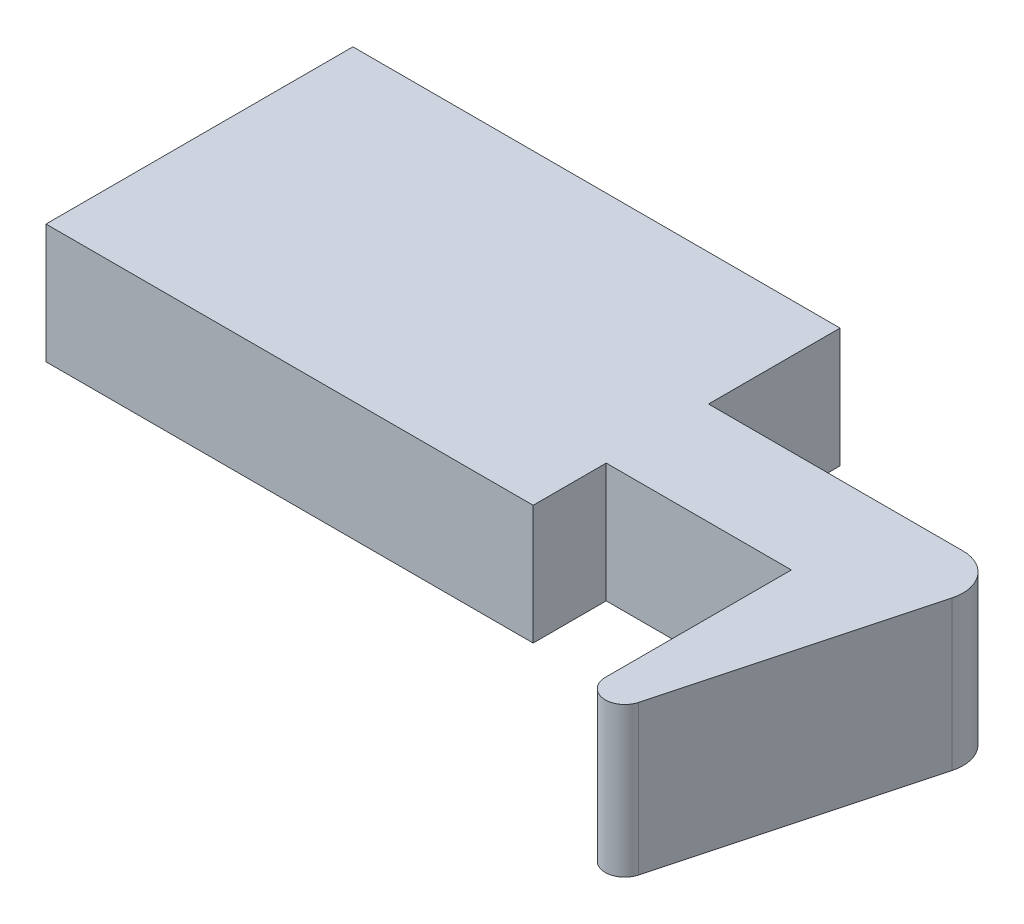
SolidWorks part; units mm, degrees
ref_plane "Front Plane" through (0, 0, 0) normal (0, 0, 1) x (1, 0, 0)
ref_plane "Top Plane" through (0, 0, 0) normal (0, 1, 0) x (1, 0, 0)
ref_plane "Right Plane" through (0, 0, 0) normal (1, 0, 0) x (0, 0, -1)
sketch "Sketch2" plane through (0, 0, 0) normal (0, 1, 0) x (1, 0, 0)
  line L0 (6.096, 5.334) -> (0, -17.4166)
  line L1 (0, 0) -> (-9.652, 0)
  line L2 (0, 0) -> (0, 5.334)
  line L3 (0, 5.334) -> (-9.652, 5.334)
  line L4 (-9.652, 0) -> (-9.652, 5.334)
  line L5 (0, 5.334) -> (6.096, 5.334)
  line L6 (0, 5.334) -> (0, -17.4166)
  line L10 (-9.652, -3.81) -> (-35.052, -3.81)
  line L11 (-9.652, -3.81) -> (-9.652, 12.192)
  line L12 (-9.652, 12.192) -> (-35.052, 12.192)
  line L13 (-35.052, -3.81) -> (-35.052, 12.192)
  dimension "D1" = 5.334
  dimension "D2" = 9.652
  dimension "D3" = 6.096
  dimension "D4" = 105
  dimension "D5" = 25.4
  dimension "D6" = 16.002
  dimension "D7" = 6.858
extrude "Boss-Extrude1" add sketch "Sketch2" along normal blind 6.223 contours L13 L10 L11 L4 L12 | L4 L1 L2 L3 | L2 L6 L0 L5
fillet "Fillet1" radius 1.016 1 edges at (0, 3.1115, 17.4166)
sketch "Sketch3" plane through (0, 0, 0) normal (0, -1, 0) x (1, 0, 0)
  line L0 (0, 0) -> (0, -5.334)
  line L9 (6.096, -5.334) -> (1.9974, 9.9623)
  line L10 (0, 9.6993) -> (0, 0)
  line L11 (0, 0) -> (-9.652, 0)
  line L12 (-9.652, 0) -> (-9.652, 3.81)
  line L13 (-9.652, 3.81) -> (-35.052, 3.81)
  line L14 (-35.052, 3.81) -> (-35.052, -12.192)
  line L15 (-35.052, -12.192) -> (-9.652, -12.192)
  line L16 (-9.652, -12.192) -> (-9.652, -5.334)
  line L17 (-9.652, -5.334) -> (6.096, -5.334)
  line L18 (6.096, -5.334) -> (1.9974, 9.9623)
  line L19 (0, 9.6993) -> (0, 0)
  line L20 (0, 0) -> (-9.652, 0)
  line L21 (-9.652, 0) -> (-9.652, 3.81)
  line L22 (-9.652, 3.81) -> (-35.052, 3.81)
  line L23 (-35.052, 3.81) -> (-35.052, -12.192)
  line L24 (-35.052, -12.192) -> (-9.652, -12.192)
  line L25 (-9.652, -12.192) -> (-9.652, -5.334)
  line L26 (-9.652, -5.334) -> (6.096, -5.334)
  arc A1 (1.9974, 9.9623) -> (0, 9.6993) centre (1.016, 9.6993) ccw
  arc A2 (1.9974, 9.9623) -> (0, 9.6993) centre (1.016, 9.6993) ccw
  line M11 (6.096, -5.334) -> (1.9974, 9.9623)
  arc M12 (1.9974, 9.9623) -> (0, 9.6993) centre (1.016, 9.6993) ccw
  line M13 (0, 9.6993) -> (0, 0)
  line M20 (-9.652, -5.334) -> (6.096, -5.334)
  dimension "D1" = 0
extrude "Boss-Extrude2" add sketch "Sketch3" along normal blind 1.5748 contours L0 M13 M20 M11 M12
fillet "Fillet2" radius 1.905 1 edges at (6.096, 2.3241, -5.334)
